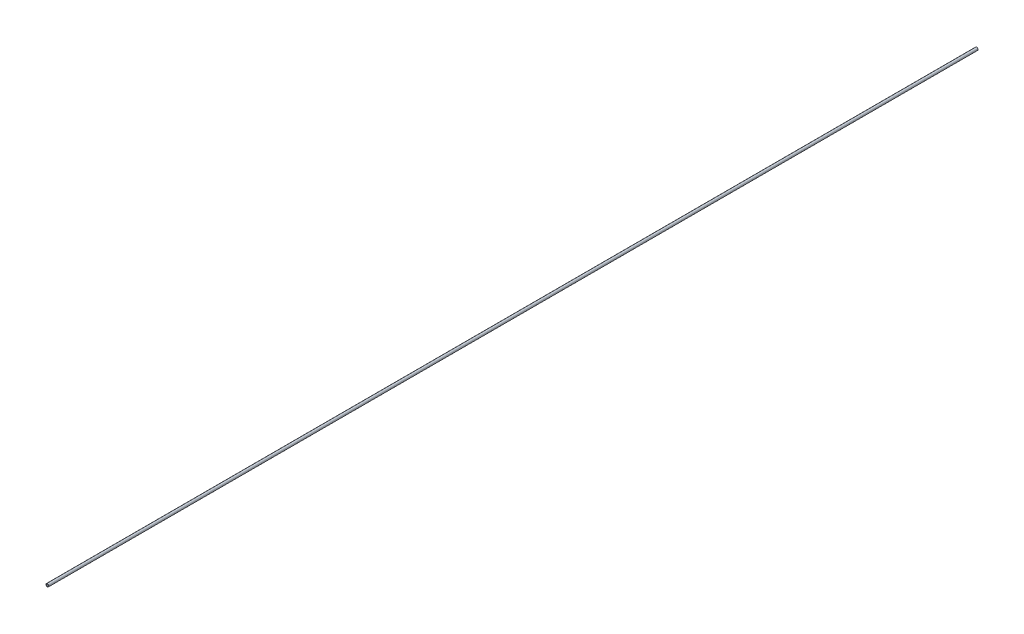
SolidWorks part; units mm, degrees
material "Carbon Fiber Tube - UD Approx"
ref_plane "Front Plane" through (0, 0, 0) normal (0, 0, 1) x (1, 0, 0)
ref_plane "Top Plane" through (0, 0, 0) normal (0, 1, 0) x (1, 0, 0)
ref_plane "Right Plane" through (0, 0, 0) normal (1, 0, 0) x (0, 0, -1)
sketch "Sketch1" plane through (0, 0, 0) normal (0, 0, 1) x (1, 0, 0)
  circle A0 centre (0, 0) radius 2
  circle A1 centre (0, 0) radius 3
  dimension "D1" = 4
  dimension "D2" = 6
extrude "Boss-Extrude1" add sketch "Sketch1" along normal blind 2000
